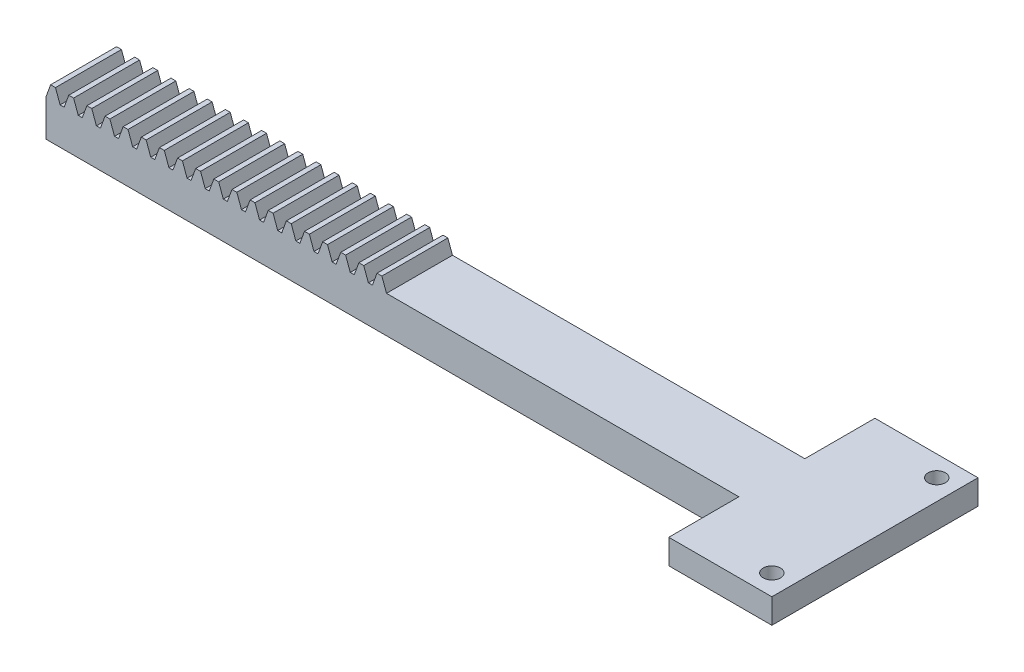
SolidWorks part; units mm, degrees
ref_plane "Plan de face" through (0, 0, 0) normal (0, 0, 1) x (1, 0, 0)
ref_plane "Plan de dessus" through (0, 0, 0) normal (0, 1, 0) x (1, 0, 0)
ref_plane "Plan de droite" through (0, 0, 0) normal (1, 0, 0) x (0, 0, -1)
ref_plane "Plan1" through (0, 0, 2) normal (0, 0, 1) x (1, 0, 0)
sketch "Esquisse1" plane through (0, 0, 2) normal (0, 0, 1) x (1, 0, 0)
  line L2 (55.972, 0) -> (140, 0)
  line L3 (140, 0) -> (140, 4.46)
  line L4 (139.0502, 4.46) -> (140, 4.46)
  line L5 (55.972, 4.46) -> (55.972, 0)
  line L205 (139.0502, 4.46) -> (138.4897, 6)
  line L206 (138.4897, 6) -> (137.8997, 6)
  line L207 (137.8997, 6) -> (137.3392, 4.46)
  line L208 (137.3392, 4.46) -> (136.8511, 4.46)
  line L209 (136.8511, 4.46) -> (136.2906, 6)
  line L210 (136.2906, 6) -> (135.7006, 6)
  line L211 (135.7006, 6) -> (135.1401, 4.46)
  line L212 (135.1401, 4.46) -> (134.652, 4.46)
  line L213 (134.652, 4.46) -> (134.0915, 6)
  line L214 (134.0915, 6) -> (133.5015, 6)
  line L215 (133.5015, 6) -> (132.9409, 4.46)
  line L216 (132.9409, 4.46) -> (132.4529, 4.46)
  line L217 (132.4529, 4.46) -> (131.8923, 6)
  line L218 (131.8923, 6) -> (131.3023, 6)
  line L219 (131.3023, 6) -> (130.7418, 4.46)
  line L220 (130.7418, 4.46) -> (130.2537, 4.46)
  line L221 (130.2537, 4.46) -> (129.6932, 6)
  line L222 (129.6932, 6) -> (129.1032, 6)
  line L223 (129.1032, 6) -> (128.5427, 4.46)
  line L224 (128.5427, 4.46) -> (128.0546, 4.46)
  line L225 (128.0546, 4.46) -> (127.4941, 6)
  line L226 (127.4941, 6) -> (126.9041, 6)
  line L227 (126.9041, 6) -> (126.3436, 4.46)
  line L228 (126.3436, 4.46) -> (125.8555, 4.46)
  line L229 (125.8555, 4.46) -> (125.295, 6)
  line L230 (125.295, 6) -> (124.705, 6)
  line L231 (124.705, 6) -> (124.1445, 4.46)
  line L232 (124.1445, 4.46) -> (123.6564, 4.46)
  line L233 (123.6564, 4.46) -> (123.0959, 6)
  line L234 (123.0959, 6) -> (122.5059, 6)
  line L235 (122.5059, 6) -> (121.9454, 4.46)
  line L236 (121.9454, 4.46) -> (121.4573, 4.46)
  line L237 (121.4573, 4.46) -> (120.8968, 6)
  line L238 (120.8968, 6) -> (120.3068, 6)
  line L239 (120.3068, 6) -> (119.7463, 4.46)
  line L240 (119.7463, 4.46) -> (119.2582, 4.46)
  line L241 (119.2582, 4.46) -> (118.6977, 6)
  line L242 (118.6977, 6) -> (118.1077, 6)
  line L243 (118.1077, 6) -> (117.5471, 4.46)
  line L244 (117.5471, 4.46) -> (117.0591, 4.46)
  line L245 (117.0591, 4.46) -> (116.4985, 6)
  line L246 (116.4985, 6) -> (115.9085, 6)
  line L247 (115.9085, 6) -> (115.348, 4.46)
  line L248 (115.348, 4.46) -> (114.8599, 4.46)
  line L249 (114.8599, 4.46) -> (114.2994, 6)
  line L250 (114.2994, 6) -> (113.7094, 6)
  line L251 (113.7094, 6) -> (113.1489, 4.46)
  line L252 (113.1489, 4.46) -> (112.6608, 4.46)
  line L253 (112.6608, 4.46) -> (112.1003, 6)
  line L254 (112.1003, 6) -> (111.5103, 6)
  line L255 (111.5103, 6) -> (110.9498, 4.46)
  line L256 (110.9498, 4.46) -> (110.4617, 4.46)
  line L257 (110.4617, 4.46) -> (109.9012, 6)
  line L258 (109.9012, 6) -> (109.3112, 6)
  line L259 (109.3112, 6) -> (108.7507, 4.46)
  line L260 (108.7507, 4.46) -> (108.2626, 4.46)
  line L261 (108.2626, 4.46) -> (107.7021, 6)
  line L262 (107.7021, 6) -> (107.1121, 6)
  line L263 (107.1121, 6) -> (106.5516, 4.46)
  line L264 (106.5516, 4.46) -> (106.0635, 4.46)
  line L265 (106.0635, 4.46) -> (105.503, 6)
  line L266 (105.503, 6) -> (104.913, 6)
  line L267 (104.913, 6) -> (104.3525, 4.46)
  line L268 (104.3525, 4.46) -> (103.8644, 4.46)
  line L269 (103.8644, 4.46) -> (103.3039, 6)
  line L270 (103.3039, 6) -> (102.7139, 6)
  line L271 (102.7139, 6) -> (102.1534, 4.46)
  line L272 (102.1534, 4.46) -> (101.6653, 4.46)
  line L273 (101.6653, 4.46) -> (101.1048, 6)
  line L274 (101.1048, 6) -> (100.5148, 6)
  line L275 (100.5148, 6) -> (99.9542, 4.46)
  line L276 (99.9542, 4.46) -> (99.4662, 4.46)
  line L277 (99.4662, 4.46) -> (98.9056, 6)
  line L278 (98.9056, 6) -> (98.3156, 6)
  line L279 (98.3156, 6) -> (97.7551, 4.46)
  line L280 (97.7551, 4.46) -> (97.267, 4.46)
  line L281 (97.267, 4.46) -> (96.7065, 6)
  line L282 (96.7065, 6) -> (96.1165, 6)
  line L283 (96.1165, 6) -> (95.556, 4.46)
  line L284 (95.556, 4.46) -> (95.0679, 4.46)
  line L285 (95.0679, 4.46) -> (94.5074, 6)
  line L286 (94.5074, 6) -> (93.9174, 6)
  line L287 (93.9174, 6) -> (93.3569, 4.46)
  line L288 (93.3569, 4.46) -> (92.8688, 4.46)
  line L289 (92.8688, 4.46) -> (92.3083, 6)
  line L290 (92.3083, 6) -> (91.7183, 6)
  line L291 (91.7183, 6) -> (91.1578, 4.46)
  line L292 (91.1578, 4.46) -> (90.6697, 4.46)
  line L293 (90.6697, 4.46) -> (90.1092, 6)
  line L294 (90.1092, 6) -> (89.5192, 6)
  line L295 (89.5192, 6) -> (88.9587, 4.46)
  line L296 (88.9587, 4.46) -> (88.4706, 4.46)
  line L297 (88.4706, 4.46) -> (87.9101, 6)
  line L298 (87.9101, 6) -> (87.3201, 6)
  line L299 (87.3201, 6) -> (86.7596, 4.46)
  line L300 (86.7596, 4.46) -> (86.2715, 4.46)
  line L301 (86.2715, 4.46) -> (85.711, 6)
  line L302 (85.711, 6) -> (85.121, 6)
  line L303 (85.121, 6) -> (84.5605, 4.46)
  line L304 (84.5605, 4.46) -> (84.0724, 4.46)
  line L305 (84.0724, 4.46) -> (83.5119, 6)
  line L306 (83.5119, 6) -> (82.9219, 6)
  line L307 (82.9219, 6) -> (82.3613, 4.46)
  line L308 (82.3613, 4.46) -> (81.8733, 4.46)
  line L309 (81.8733, 4.46) -> (81.3127, 6)
  line L310 (81.3127, 6) -> (80.7227, 6)
  line L311 (80.7227, 6) -> (80.1622, 4.46)
  line L312 (80.1622, 4.46) -> (79.6741, 4.46)
  line L313 (79.6741, 4.46) -> (79.1136, 6)
  line L314 (79.1136, 6) -> (78.5236, 6)
  line L315 (78.5236, 6) -> (77.9631, 4.46)
  line L316 (77.9631, 4.46) -> (77.475, 4.46)
  line L317 (77.475, 4.46) -> (76.9145, 6)
  line L318 (76.9145, 6) -> (76.3245, 6)
  line L319 (76.3245, 6) -> (75.764, 4.46)
  line L320 (75.764, 4.46) -> (75.2759, 4.46)
  line L321 (75.2759, 4.46) -> (74.7154, 6)
  line L322 (74.7154, 6) -> (74.1254, 6)
  line L323 (74.1254, 6) -> (73.5649, 4.46)
  line L324 (73.5649, 4.46) -> (73.0768, 4.46)
  line L325 (73.0768, 4.46) -> (72.5163, 6)
  line L326 (72.5163, 6) -> (71.9263, 6)
  line L327 (71.9263, 6) -> (71.3658, 4.46)
  line L328 (71.3658, 4.46) -> (70.8777, 4.46)
  line L329 (70.8777, 4.46) -> (70.3172, 6)
  line L330 (70.3172, 6) -> (69.7272, 6)
  line L331 (69.7272, 6) -> (69.1667, 4.46)
  line L332 (69.1667, 4.46) -> (68.6786, 4.46)
  line L333 (68.6786, 4.46) -> (68.1181, 6)
  line L334 (68.1181, 6) -> (67.5281, 6)
  line L335 (67.5281, 6) -> (66.9675, 4.46)
  line L336 (66.9675, 4.46) -> (66.4795, 4.46)
  line L337 (66.4795, 4.46) -> (65.9189, 6)
  line L338 (65.9189, 6) -> (65.3289, 6)
  line L339 (65.3289, 6) -> (64.7684, 4.46)
  line L340 (64.7684, 4.46) -> (64.2803, 4.46)
  line L341 (64.2803, 4.46) -> (63.7198, 6)
  line L342 (63.7198, 6) -> (63.1298, 6)
  line L343 (63.1298, 6) -> (62.5693, 4.46)
  line L344 (62.5693, 4.46) -> (62.0812, 4.46)
  line L345 (62.0812, 4.46) -> (61.5207, 6)
  line L346 (61.5207, 6) -> (60.9307, 6)
  line L347 (60.9307, 6) -> (60.3702, 4.46)
  line L348 (60.3702, 4.46) -> (59.8821, 4.46)
  line L349 (59.8821, 4.46) -> (59.3216, 6)
  line L350 (59.3216, 6) -> (58.7316, 6)
  line L351 (58.7316, 6) -> (58.1711, 4.46)
  line L352 (58.1711, 4.46) -> (57.683, 4.46)
  line L353 (57.683, 4.46) -> (57.1225, 6)
  line L354 (57.1225, 6) -> (56.5325, 6)
  line L355 (56.5325, 6) -> (55.972, 4.46)
extrude "Boss.-Extru.1" add sketch "Esquisse1" against normal blind 8
sketch "Esquisse3" plane through (140, 0, 0) normal (1, 0, 0) x (0, 0, -1)
  line L1 (-10.5, 4.46) -> (14.5, 4.46)
  line L2 (-10.5, 4.46) -> (-10.5, 1.46)
  line L3 (-10.5, 1.46) -> (14.5, 1.46)
  line L4 (14.5, 4.46) -> (14.5, 1.46)
  line L9 (-2, 55) -> (-2, -55) construction
  dimension "D1" = 3
  dimension "D2" = 25
  dimension "D3" = 8.5
extrude "Boss.-Extru.3" add sketch "Esquisse3" along normal blind 12.5
sketch "Esquisse4" plane through (0, 4.46, 0) normal (0, 1, 0) x (1, 0, 0)
  line L0 (152.5, -10.5) -> (140, -10.5) construction
  line L1 (140, -2) -> (140, -10.5) construction
  circle A0 centre (150, -8) radius 1.05
  circle A1 centre (150, 12) radius 1.05
  dimension "D1" = 2.1
  dimension "D2" = 2.1
  dimension "D4" = 2.5
  dimension "D5" = 10
  dimension "D3" = 20
extrude "Enlèv. mat.-Extru.1" cut sketch "Esquisse4" against normal blind 10
sketch "Esquisse7" plane through (152.5, 0, 0) normal (1, 0, 0) x (0, 0, -1)
  line L1 (-4.6487, 4.46) -> (9.0541, 4.46)
  line L2 (-4.6487, 4.46) -> (-4.6487, 11.7437)
  line L3 (-4.6487, 11.7437) -> (9.0541, 11.7437)
  line L4 (9.0541, 4.46) -> (9.0541, 11.7437)
  line L5 (14.5, 4.46) -> (-10.5, 4.46) construction
extrude "Enlèv. mat.-Extru.2" cut sketch "Esquisse7" against normal blind 55
